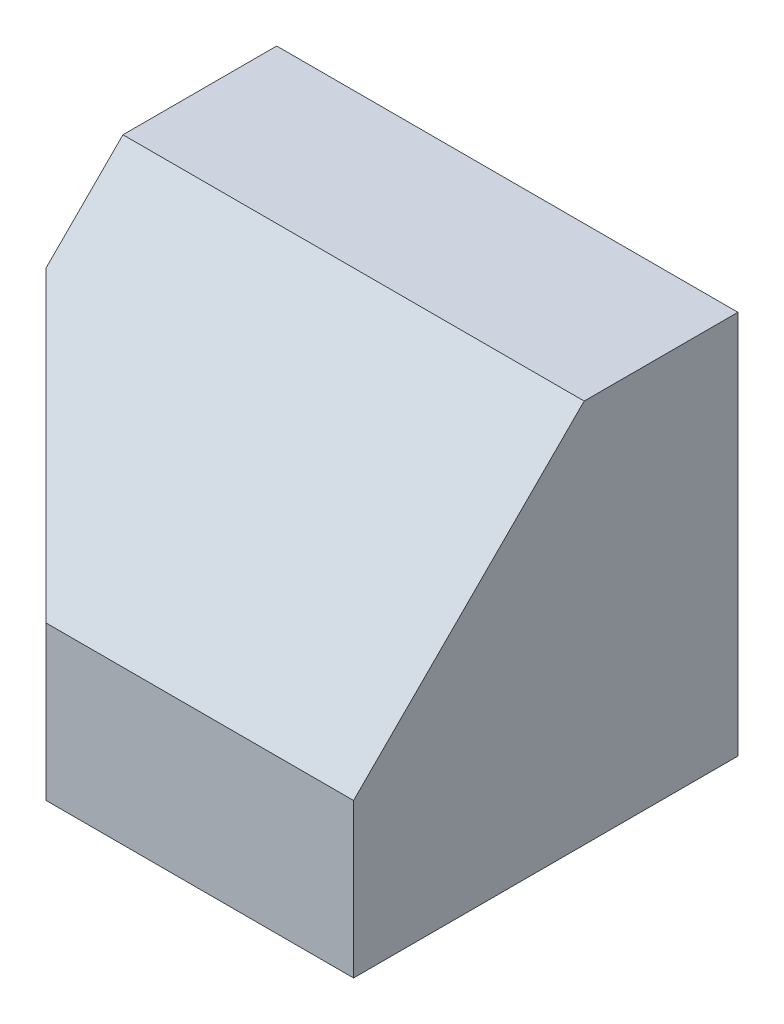
SolidWorks part; units mm, degrees
ref_plane "Front Plane" through (0, 0, 0) normal (0, 0, 1) x (1, 0, 0)
ref_plane "Top Plane" through (0, 0, 0) normal (0, 1, 0) x (1, 0, 0)
ref_plane "Right Plane" through (0, 0, 0) normal (1, 0, 0) x (0, 0, -1)
sketch "Sketch1" plane through (0, 0, 0) normal (0, 0, 1) x (1, 0, 0)
  line L1 (0, 0) -> (60, 0)
  line L2 (0, 0) -> (0, 50)
  line L3 (0, 50) -> (60, 50)
  line L4 (60, 0) -> (60, 50)
  dimension "D1" = 60
  dimension "D2" = 50
extrude "Boss-Extrude1" add sketch "Sketch1" along normal blind 50
sketch "Sketch2" plane through (0, 0, 0) normal (0, -1, 0) x (1, 0, 0)
  line L0 (0, 30) -> (20, 50)
  line L1 (0, 50) -> (0, 0) construction
  line L2 (0, 50) -> (60, 50) construction
  line L3 (20, 50) -> (0, 50)
  line L4 (0, 50) -> (0, 30)
  dimension "D1" = 20
  dimension "D2" = 20
extrude "Cut-Extrude1" cut sketch "Sketch2" against normal blind 50
sketch "Sketch3" plane through (0, 0, 50) normal (0, 0, 1) x (1, 0, 0)
  line L1 (60, 50) -> (0, 50)
  line L2 (60, 50) -> (60, 20)
  line L3 (60, 20) -> (0, 20)
  line L4 (0, 50) -> (0, 20)
  dimension "D1" = 30
  dimension "D2" = 60
extrude "Cut-Extrude2" cut sketch "Sketch3" against normal blind 30
ref_plane "Plane1" through (0, 35, 35) normal (0, 0.7071, 0.7071) x (1, 0, 0)
sketch "Sketch4" plane through (0, 35, 35) normal (0, 0.7071, 0.7071) x (1, 0, 0)
  line L0 (60, -21.2132) -> (60, 21.2132)
  line L1 (60, 21.2132) -> (0, 21.2132)
  line L2 (0, 21.2132) -> (20, -21.2132)
  line L3 (20, -21.2132) -> (60, -21.2132)
extrude "Boss-Extrude2" add sketch "Sketch4" against normal blind 30
ref_plane "Plane2" through (-9.2308, 0, 6.1538) normal (-0.8321, 0, 0.5547) x (0.5547, 0, 0.8321)
ref_plane "Plane3" through (-17.3684, 5.7895, 17.3684) normal (0.6882, -0.2294, -0.6882) x (-0.6529, 0.2176, -0.7255)
sketch "Sketch9" plane through (0, 0, 0) normal (0, 0, -1) x (-1, 0, 0)
  line L1 (-60, 50) -> (0, 50)
  line L2 (-60, 50) -> (-60, 0)
  line L3 (-60, 0) -> (0, 0)
  line L4 (0, 50) -> (0, 0)
extrude "Cut-Extrude3" cut sketch "Sketch9" along normal blind 10
sketch "Sketch10" plane through (0, 0, 0) normal (0, -1, 0) x (1, 0, 0)
  line L1 (60, 0) -> (0, 0)
  line L2 (60, 0) -> (60, 30)
  line L3 (60, 30) -> (0, 30)
  line L4 (0, 0) -> (0, 30)
extrude "Cut-Extrude4" cut sketch "Sketch10" along normal blind 10
sketch "Sketch18" plane through (0, 20, 0) normal (0, 1, 0) x (1, 0, 0)
  line L0 (10, -20) -> (0, -20)
  line L1 (0, -20) -> (0, -30)
  line L2 (0, -30) -> (20, -50)
  line L3 (20, -50) -> (10, -20)
extrude "Boss-Extrude7" add sketch "Sketch18" along normal blind 30
sketch "Sketch19" plane through (3, 0, -1) normal (0.9487, 0, -0.3162) x (-0.3162, 0, -0.9487)
  line L0 (-22.1359, 50) -> (-53.7587, 20)
  line L1 (-53.7587, 20) -> (-53.7587, 50)
  line L2 (-53.7587, 50) -> (-22.1359, 50)
extrude "Cut-Extrude10" cut sketch "Sketch19" against normal blind 30
sketch "Sketch20" plane through (0, 35, 35) normal (0, 0.7071, 0.7071) x (1, 0, 0)
  line L0 (60, 21.2132) -> (0, 21.2132)
  line L1 (0, 21.2132) -> (0, -21.2132)
  line L2 (0, -21.2132) -> (60, -21.2132)
  line L3 (60, -21.2132) -> (60, 21.2132)
  dimension "D1" = 60
extrude "Cut-Extrude11" cut sketch "Sketch20" along normal blind 30
